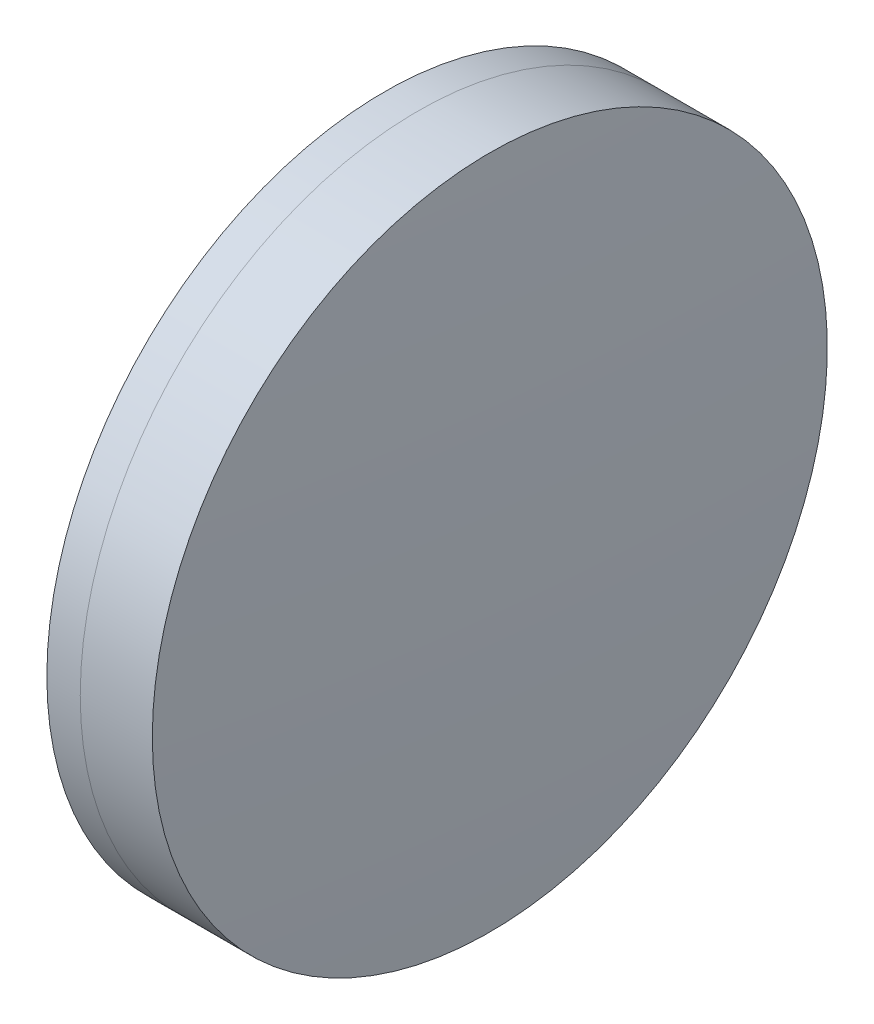
SolidWorks part; units mm, degrees
ref_plane "前视基准面" through (0, 0, 0) normal (0, 0, 1) x (1, 0, 0)
ref_plane "上视基准面" through (0, 0, 0) normal (0, 1, 0) x (1, 0, 0)
ref_plane "右视基准面" through (0, 0, 0) normal (1, 0, 0) x (0, 0, -1)
sketch "草图1" plane through (0, 0, 0) normal (0, 1, 0) x (1, 0, 0)
  line L0 (124.5233, 0) -> (646.9917, 0) construction
  line L1 (300.9207, -12.7) -> (302.1767, -12.7)
  line L2 (300.9207, 12.7) -> (302.1767, 12.7)
  arc A0 (302.1767, -12.7) -> (302.1767, 12.7) centre (250.0001, 0) ccw
  arc A1 (300.9207, 12.7) -> (300.9207, -12.7) centre (366.3801, 0) ccw
  point P10 (299.7001, 0)
  point P11 (303.7001, 0)
  dimension "D3" = 66.68
  dimension "D4" = 53.7
  dimension "D1" = 12.7
  dimension "D2" = 12.7
  dimension "D5" = 4
revolve "旋转1" add sketch "草图1" angle 360 about L0
sketch "草图2" plane through (0, 0, 0) normal (0, 1, 0) x (1, 0, 0)
  line L0 (-0.5519, 0) -> (622.6607, 0) construction
  line L2 (302.1767, 12.7) -> (304.8891, 12.7)
  line L3 (302.1767, -12.7) -> (304.8891, -12.7)
  arc A0 (304.8891, -12.7) -> (304.8891, 12.7) centre (45.7901, 0) ccw
  arc A1 (302.1767, -12.7) -> (302.1767, 12.7) centre (250.0001, 0) ccw construction
  arc A2 (302.1767, -12.7) -> (302.1767, 12.7) centre (250.0001, 0) ccw
  point P4 (303.7001, 0)
  point P8 (305.2001, 0)
  dimension "D1" = 259.41
  dimension "D2" = 1.5
revolve "旋转3" add sketch "草图2" angle 360 about L0
